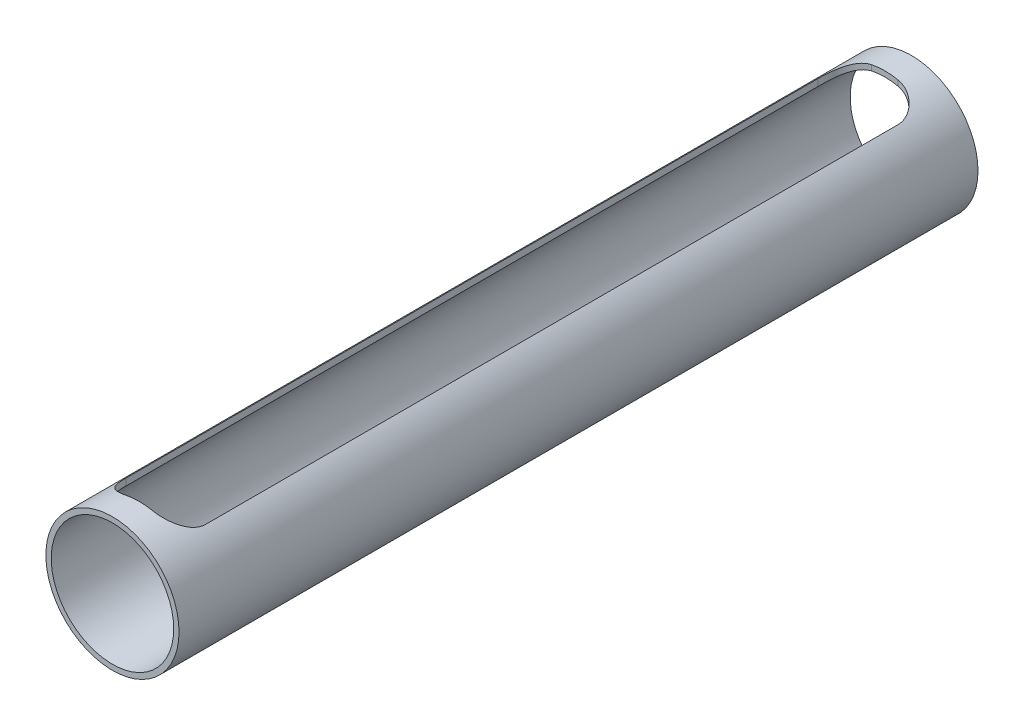
SolidWorks part; units mm, degrees
material "PVC Rigid"
ref_plane "Front Plane" through (0, 0, 0) normal (0, 0, 1) x (1, 0, 0)
ref_plane "Top Plane" through (0, 0, 0) normal (0, 1, 0) x (1, 0, 0)
ref_plane "Right Plane" through (0, 0, 0) normal (1, 0, 0) x (0, 0, -1)
sketch "Sketch1" plane through (0, 0, 0) normal (0, 0, 1) x (1, 0, 0)
  circle A0 centre (0, 0) radius 25
  circle A1 centre (0, 0) radius 23
  dimension "D1" = 50
  dimension "D2" = 2
extrude "Boss-Extrude1" add sketch "Sketch1" along normal blind 300
ref_plane "Plane1" through (0, 50, 0) normal (0, 1, 0) x (1, 0, 0)
sketch "Sketch2" plane through (0, 50, 0) normal (0, 1, 0) x (1, 0, 0)
  line L0 (5, -10) -> (-5, -10)
  line L1 (-15, -20) -> (-15, -280)
  line L2 (-5, -290) -> (5, -290)
  line L3 (15, -280) -> (15, -20)
  line L4 (25, 0) -> (-25, 0) construction
  arc A0 (5, -10) -> (15, -20) centre (5, -20) cw
  arc A1 (-5, -10) -> (-15, -20) centre (-5, -20) ccw
  arc A2 (5, -290) -> (15, -280) centre (5, -280) ccw
  arc A3 (-5, -290) -> (-15, -280) centre (-5, -280) cw
  point P2 (0, 0)
  point P5 (0, -10)
  point P6 (0, -8.7495)
  point P7 (0, 0)
  point P8 (0, 0)
  point P11 (15, -150)
  point P16 (15, -10)
  point P19 (-15, -10)
  dimension "D5" = 10
  dimension "D1" = 0
  dimension "D2" = 30
  dimension "D3" = 150
  dimension "D4" = 10
extrude "Cut-Extrude1" cut sketch "Sketch2" against normal blind 51
